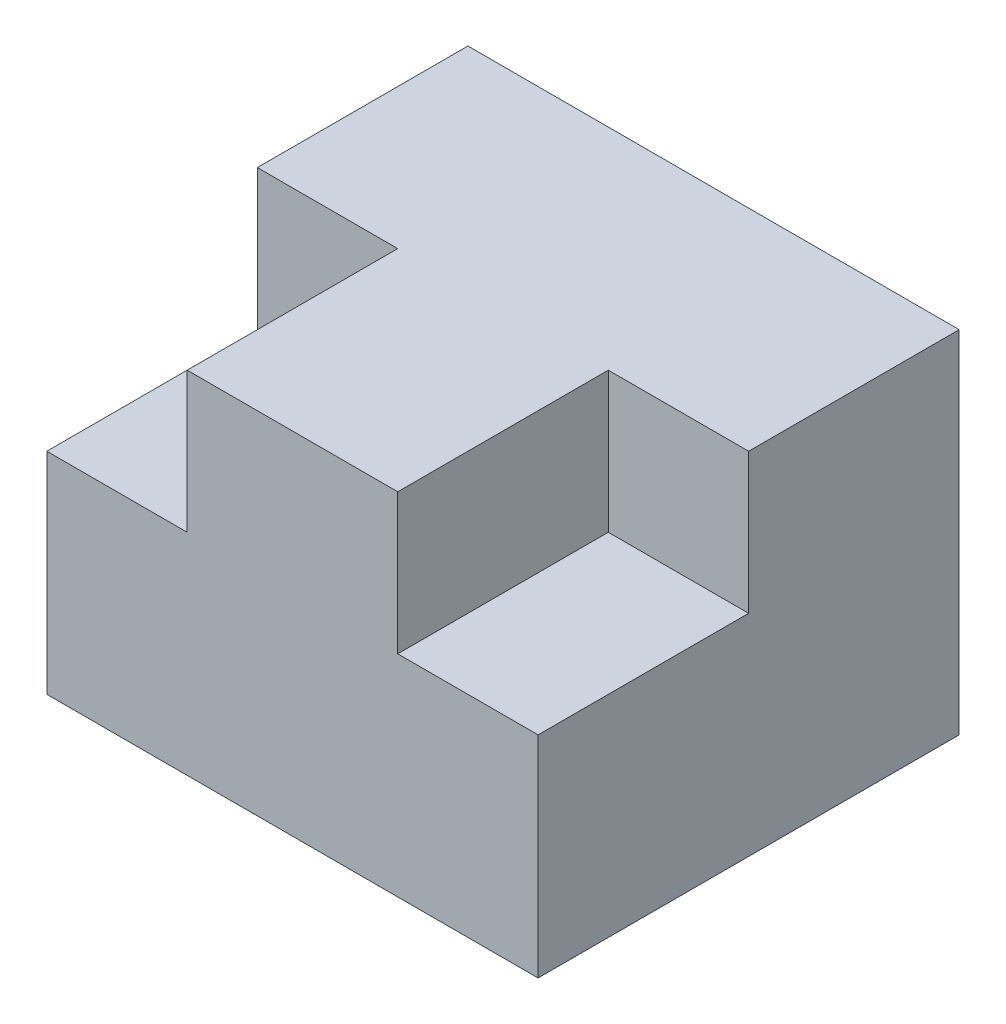
SolidWorks part; units mm, degrees
ref_plane "Front Plane" through (0, 0, 0) normal (0, 0, 1) x (1, 0, 0)
ref_plane "Top Plane" through (0, 0, 0) normal (0, 1, 0) x (1, 0, 0)
ref_plane "Right Plane" through (0, 0, 0) normal (1, 0, 0) x (0, 0, -1)
sketch "Sketch1" plane through (0, 0, 0) normal (0, 0, 1) x (1, 0, 0)
  line L1 (-23.2779, 12.5399) -> (11.7221, 12.5399)
  line L2 (-23.2779, 12.5399) -> (-23.2779, -12.4601)
  line L3 (-23.2779, -12.4601) -> (11.7221, -12.4601)
  line L4 (11.7221, 12.5399) -> (11.7221, -12.4601)
  dimension "D1" = 25
  dimension "D2" = 35
extrude "Boss-Extrude1" add sketch "Sketch1" against normal blind 15
sketch "Sketch2" plane through (0, 0, 0) normal (0, 0, 1) x (1, 0, 0)
  line L1 (11.7221, 12.5399) -> (-23.2779, 12.5399) construction
  line L2 (-13.2779, 12.5399) -> (1.7221, 12.5399)
  line L3 (-23.2779, -12.4601) -> (11.7221, -12.4601)
  line L4 (11.7221, -12.4601) -> (11.7221, 2.5399)
  line L5 (11.7221, -12.4601) -> (11.7221, 12.5399) construction
  line L6 (11.7221, 2.5399) -> (1.7221, 2.5399)
  line L7 (1.7221, 2.5399) -> (1.7221, 12.5399)
  line L9 (-23.2779, -12.4601) -> (-23.2779, 2.5399)
  line L10 (-23.2779, 2.5399) -> (-13.2779, 2.5399)
  line L11 (-13.2779, 2.5399) -> (-13.2779, 12.5399)
extrude "Boss-Extrude2" add sketch "Sketch2" along normal blind 15
